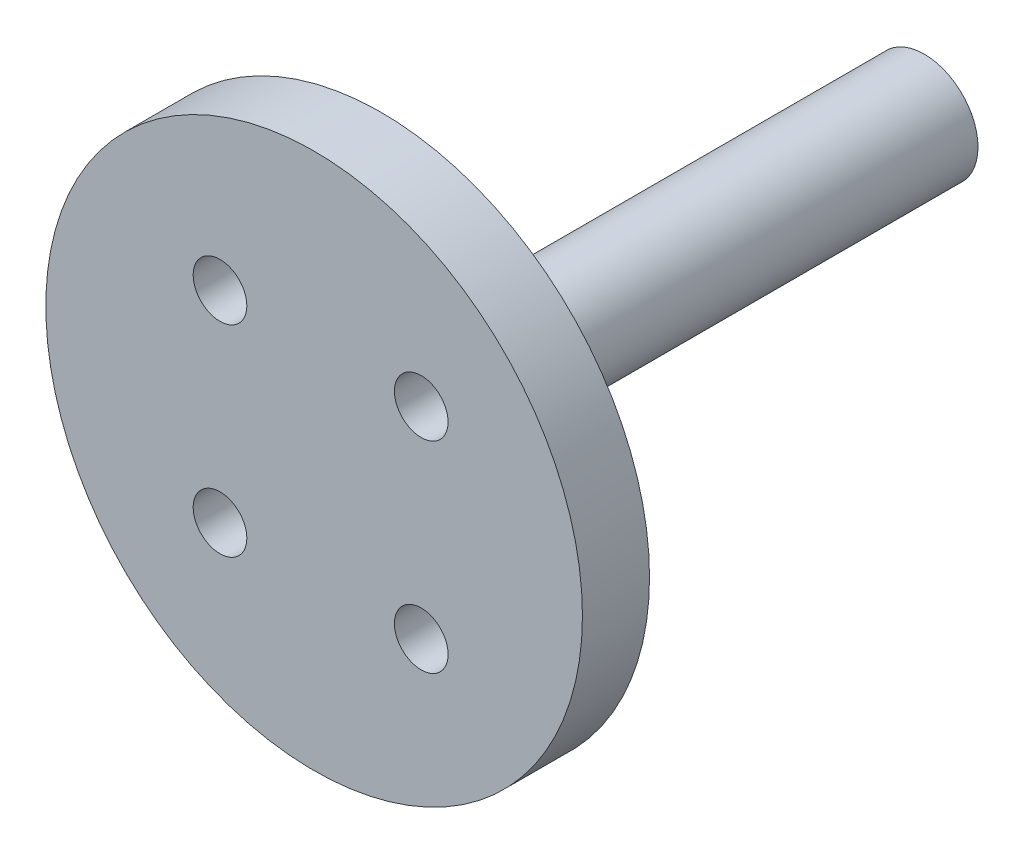
SolidWorks part; units mm, degrees
ref_plane "Front Plane" through (0, 0, 0) normal (0, 0, 1) x (1, 0, 0)
ref_plane "Top Plane" through (0, 0, 0) normal (0, 1, 0) x (1, 0, 0)
ref_plane "Right Plane" through (0, 0, 0) normal (1, 0, 0) x (0, 0, -1)
sketch "Sketch1" plane through (0, 0, 0) normal (0, 0, 1) x (1, 0, 0)
  circle A2 centre (-0.4838, 0) radius 20
  dimension "D3" = 40
extrude "Boss-Extrude1" add sketch "Sketch1" along normal blind 5
sketch "Sketch2" plane through (0, 0, 0) normal (0, 0, -1) x (-1, 0, 0)
  line L5 (-7.5, 7.5) -> (7.5, -7.5) construction
  line L6 (-7.5, -7.5) -> (6.0858, 6.0858) construction
  circle A0 centre (7.5, 7.5) radius 2
  circle A1 centre (7.5, -7.5) radius 2
  circle A2 centre (-7.5, -7.5) radius 2
  circle A3 centre (-7.5, 7.5) radius 2
  point P0 (0, 0)
  dimension "D3" = 4
  dimension "D4" = 4
  dimension "D5" = 4
  dimension "D6" = 4
  dimension "D1" = 15
  dimension "D2" = 15
extrude "Cut-Extrude1" cut sketch "Sketch2" against normal blind 30 contours A3 | A0 | A1 | A2
sketch "Sketch3" plane through (0, 0, 0) normal (0, 0, -1) x (-1, 0, 0)
  circle A0 centre (0, 0) radius 4
  dimension "D1" = 8
extrude "Boss-Extrude3" add sketch "Sketch3" along normal blind 40
sketch "Sketch4" plane through (0, 0, -40) normal (0, 0, -1) x (-1, 0, 0)
  circle A0 centre (0, 0) radius 2.5
  dimension "D1" = 5
extrude "Cut-Extrude2" cut sketch "Sketch4" against normal blind 16
